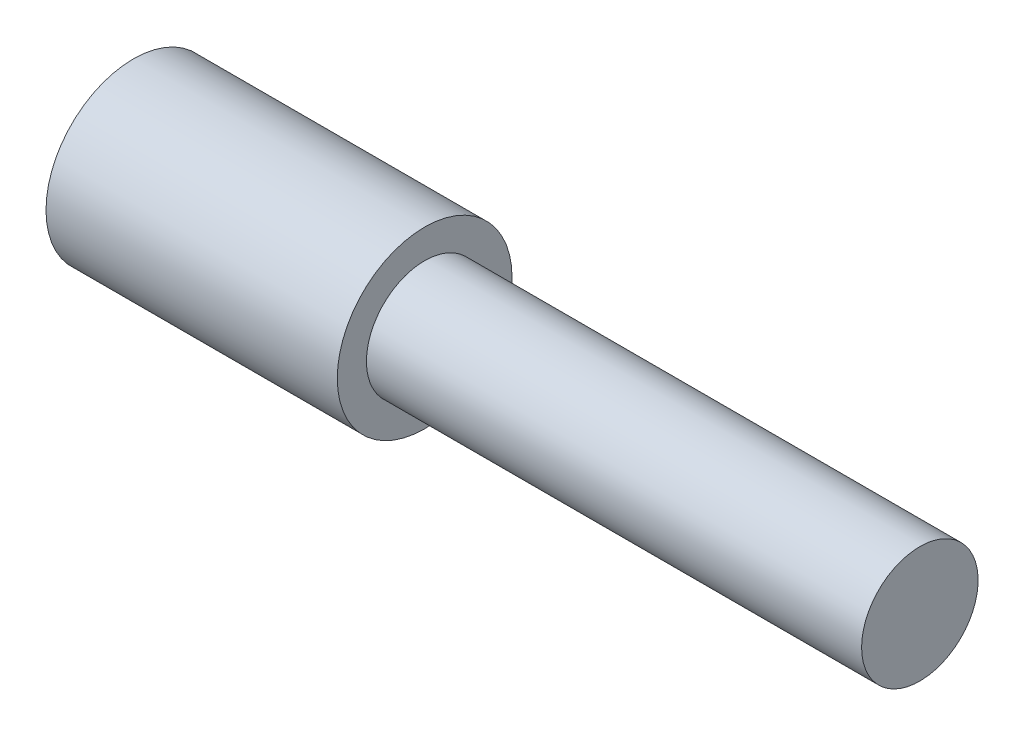
SolidWorks part; units mm, degrees
ref_plane "Plan de face" through (0, 0, 0) normal (0, 0, 1) x (1, 0, 0)
ref_plane "Plan de dessus" through (0, 0, 0) normal (0, 1, 0) x (1, 0, 0)
ref_plane "Plan de droite" through (0, 0, 0) normal (1, 0, 0) x (0, 0, -1)
sketch "Esquisse1" plane through (0, 0, 0) normal (0, 0, 1) x (1, 0, 0)
  line L0 (27, 0) -> (27, 2)
  line L1 (27, 2) -> (10, 2)
  line L2 (10, 2) -> (10, 3)
  line L3 (10, 3) -> (0, 3)
  line L4 (0, 3) -> (0, 0)
  line L5 (0, 0) -> (27, 0)
  dimension "D1" = 2
  dimension "D2" = 3
  dimension "D3" = 10
  dimension "D4" = 17
revolve "Révolution1" add sketch "Esquisse1" angle 360 about L5
